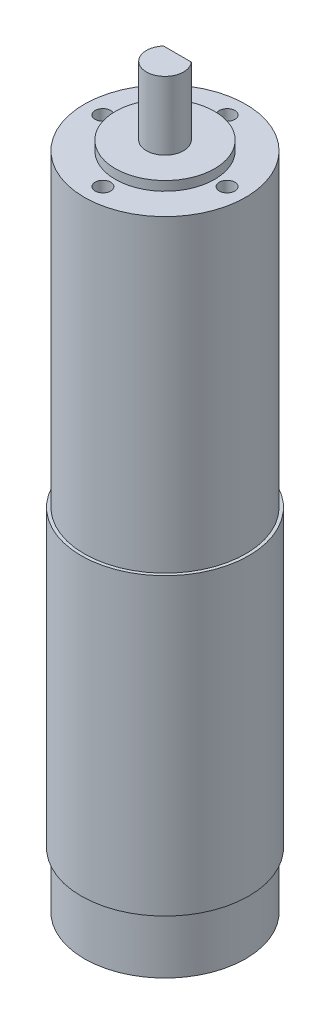
SolidWorks part; units mm, degrees
ref_plane "Front Plane" through (0, 0, 0) normal (0, 0, 1) x (1, 0, 0)
ref_plane "Top Plane" through (0, 0, 0) normal (0, 1, 0) x (1, 0, 0)
ref_plane "Right Plane" through (0, 0, 0) normal (1, 0, 0) x (0, 0, -1)
sketch "Sketch1" plane through (0, 0, 0) normal (0, 1, 0) x (1, 0, 0)
  circle A0 centre (0, 0) radius 27
  dimension "D1" = 54
extrude "Boss-Extrude1" add sketch "Sketch1" along normal blind 95
sketch "Sketch2" plane through (0, 95, 0) normal (0, 1, 0) x (1, 0, 0)
  circle A0 centre (0, 0) radius 26
  dimension "D1" = 52
extrude "Boss-Extrude2" add sketch "Sketch2" along normal blind 99.5
sketch "Sketch3" plane through (0, 194.5, 0) normal (0, 1, 0) x (1, 0, 0)
  circle A0 centre (0, 0) radius 16
  dimension "D1" = 32
extrude "Boss-Extrude3" add sketch "Sketch3" along normal blind 3
sketch "Sketch4" plane through (0, 197.5, 0) normal (0, 1, 0) x (1, 0, 0)
  circle A0 centre (0, 0) radius 6
  dimension "D1" = 12
extrude "Boss-Extrude4" add sketch "Sketch4" along normal blind 22
sketch "Sketch5" plane through (0, 219.5, 0) normal (0, 1, 0) x (1, 0, 0)
  line L0 (-4.4721, 4) -> (4.4721, 4)
  arc A0 (4.4721, 4) -> (-4.4721, 4) centre (0, 0) ccw
  circle A1 centre (0, 0) radius 6 construction
  dimension "D1" = 4
extrude "Cut-Extrude1" cut sketch "Sketch5" against normal blind 15
sketch "Sketch6" plane through (0, 194.5, 0) normal (0, 1, 0) x (1, 0, 0)
  circle A0 centre (0, 0) radius 20 construction
  circle A1 centre (0, 20) radius 2.5
  circle A2 centre (-20, 0) radius 2.5
  circle A3 centre (0, -20) radius 2.5
  circle A4 centre (20, 0) radius 2.5
  dimension "D1" = 40
  dimension "D2" = 5
  dimension "D3" = 5
  dimension "D4" = 5
  dimension "D5" = 5
extrude "Cut-Extrude2" cut sketch "Sketch6" against normal blind 10
sketch "Sketch7" plane through (0, 0, 0) normal (0, -1, 0) x (1, 0, 0)
  circle A0 centre (0, 0) radius 26
  dimension "D1" = 52
extrude "Boss-Extrude5" add sketch "Sketch7" along normal blind 18
